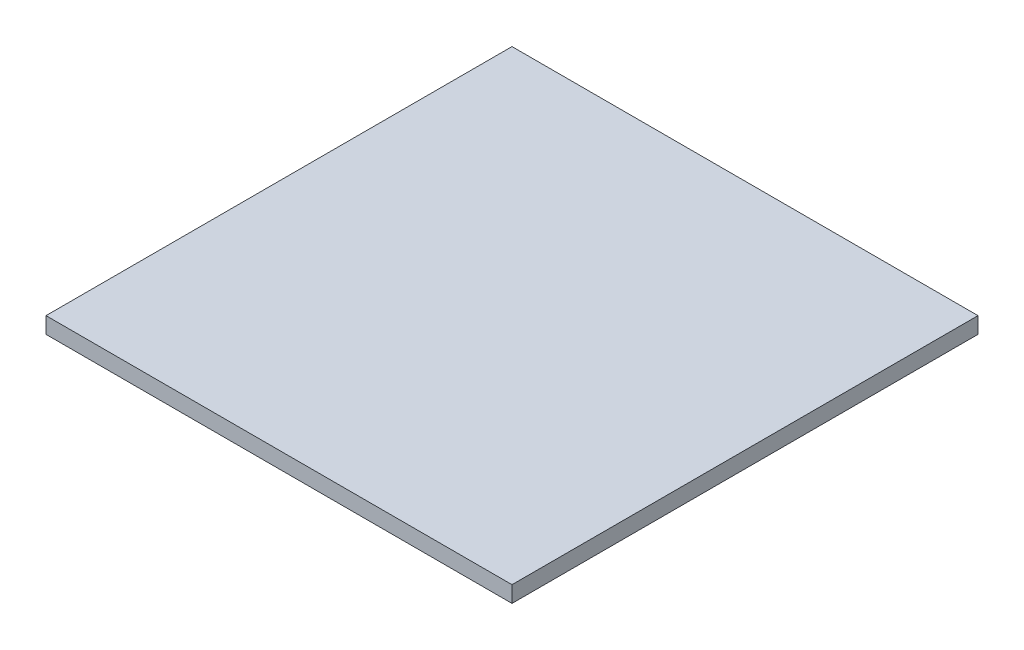
SolidWorks part; units mm, degrees
ref_plane "Front Plane" through (0, 0, 0) normal (0, 0, 1) x (1, 0, 0)
ref_plane "Top Plane" through (0, 0, 0) normal (0, 1, 0) x (1, 0, 0)
ref_plane "Right Plane" through (0, 0, 0) normal (1, 0, 0) x (0, 0, -1)
sketch "Sketch1" plane through (0, 0, 0) normal (0, 1, 0) x (1, 0, 0)
  line L1 (-17.5, -17.5) -> (17.5, -17.5)
  line L2 (-17.5, -17.5) -> (-17.5, 17.5)
  line L3 (-17.5, 17.5) -> (17.5, 17.5)
  line L4 (17.5, -17.5) -> (17.5, 17.5)
  line L5 (-17.5, -17.5) -> (17.5, 17.5) construction
  line L6 (-17.5, 17.5) -> (17.5, -17.5) construction
  point P0 (0, 0)
  dimension "D1" = 35
extrude "Boss-Extrude1" add sketch "Sketch1" along normal blind 1.22
